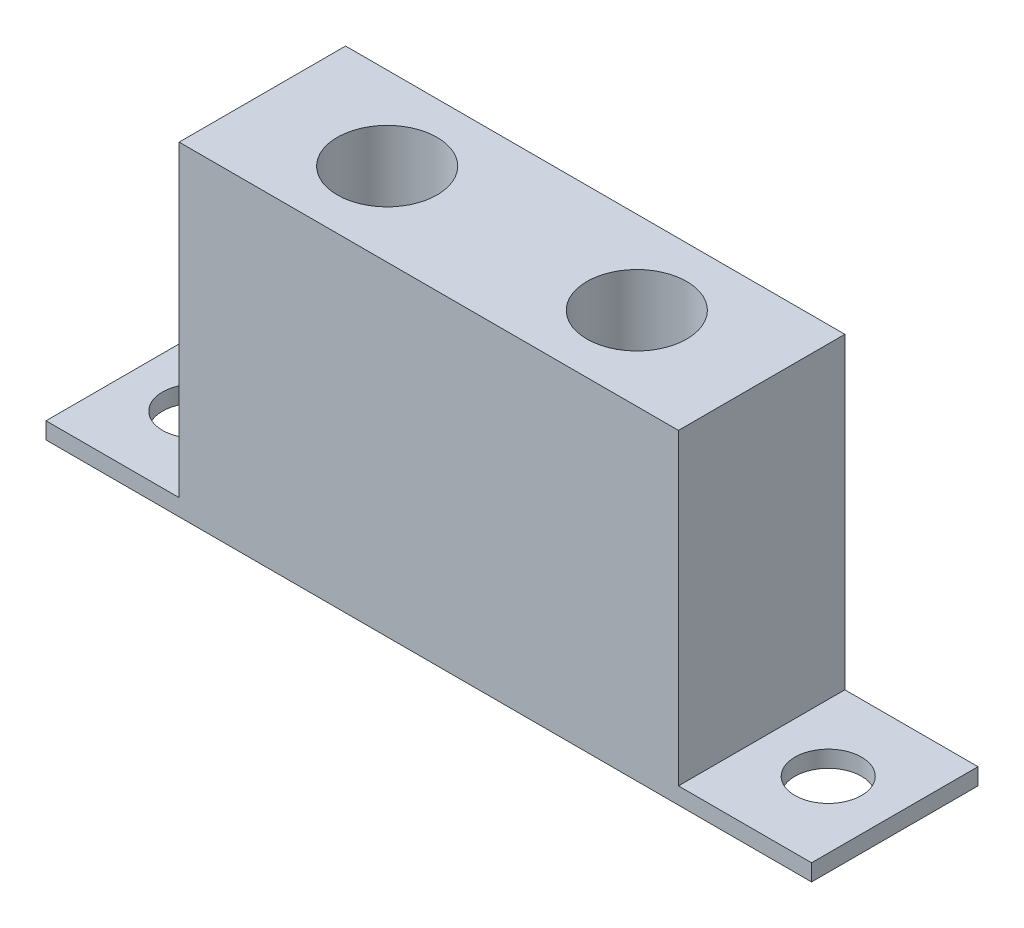
SolidWorks part; units mm, degrees
ref_plane "Front" through (0, 0, 0) normal (0, 0, 1) x (1, 0, 0)
ref_plane "Top" through (0, 0, 0) normal (0, 1, 0) x (1, 0, 0)
ref_plane "Right" through (0, 0, 0) normal (1, 0, 0) x (0, 0, -1)
sketch "Sketch1" plane through (0, 0, 0) normal (0, 1, 0) x (1, 0, 0)
  line L1 (-7.8417, -2.5) -> (7.1583, -2.5)
  line L2 (-7.8417, -2.5) -> (-7.8417, 2.5)
  line L3 (-7.8417, 2.5) -> (7.1583, 2.5)
  line L4 (7.1583, -2.5) -> (7.1583, 2.5)
  line L5 (-7.8417, -2.5) -> (7.1583, 2.5) construction
  line L6 (-7.8417, 2.5) -> (7.1583, -2.5) construction
  point P0 (0, 0)
  dimension "D1" = 5
  dimension "D2" = 15
extrude "Boss-Extrude1" add sketch "Sketch1" along normal blind 9.75
sketch "Sketch2" plane through (0, 9.75, 0) normal (0, 1, 0) x (1, 0, 0)
  line L0 (-7.8417, 2.5) -> (-7.8417, -2.5) construction
  line L1 (7.1583, -2.5) -> (7.1583, 2.5) construction
  circle A0 centre (-4.0917, 0) radius 1.5
  circle A1 centre (3.4083, 0) radius 1.5
  dimension "D1" = 3
  dimension "D2" = 3
  dimension "D3" = 3.75
  dimension "D4" = 3.75
extrude "Cut-Extrude1" cut sketch "Sketch2" against normal blind 4
sketch "Sketch3" plane through (7.1583, 0, 0) normal (1, 0, 0) x (0, 0, -1)
  line L0 (2.75, 0) -> (-2.75, 0) construction
  line L1 (-2.5, 0) -> (2.5, 0)
  line L2 (-2.5, 0) -> (-2.5, 0.5)
  line L3 (-2.5, 0.5) -> (2.5, 0.5)
  line L4 (2.5, 0) -> (2.5, 0.5)
  dimension "D1" = 90
  dimension "D2" = 0.5
extrude "Boss-Extrude2" add sketch "Sketch3" along normal blind 4
sketch "Sketch4" plane through (-7.8417, 0, 0) normal (-1, 0, 0) x (0, 0, 1)
  line L1 (-2.5, 0) -> (2.5, 0)
  line L2 (-2.5, 0) -> (-2.5, 0.5)
  line L3 (-2.5, 0.5) -> (2.5, 0.5)
  line L4 (2.5, 0) -> (2.5, 0.5)
  dimension "D1" = 0.5
extrude "Boss-Extrude3" add sketch "Sketch4" along normal blind 4
sketch "Sketch5" plane through (0, 0.5, 0) normal (0, 1, 0) x (1, 0, 0)
  line L1 (-11.8417, -2.5) -> (-11.8417, 2.5) construction
  line L2 (11.1583, 2.5) -> (11.1583, -2.5) construction
  circle A0 centre (-9.8417, 0) radius 1
  circle A1 centre (9.1583, 0) radius 1
  dimension "D1" = 2
  dimension "D3" = 2
  dimension "D2" = 2
  dimension "D4" = 2
extrude "Cut-Extrude2" cut sketch "Sketch5" against normal blind 4
